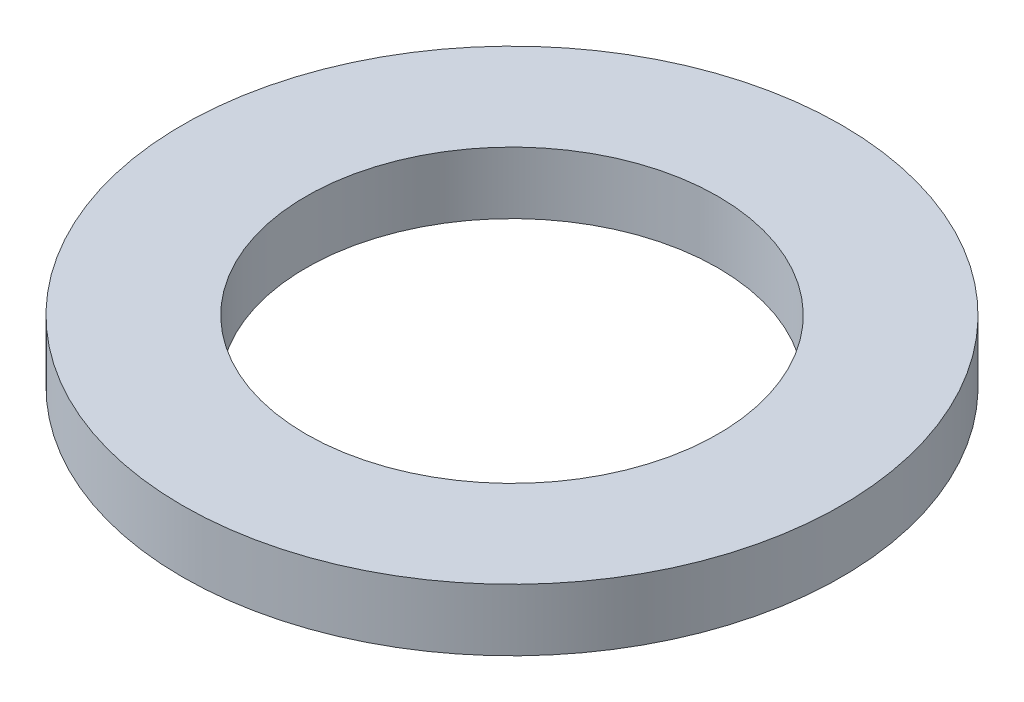
SolidWorks part; units mm, degrees
ref_plane "Front Plane" through (0, 0, 0) normal (0, 0, 1) x (1, 0, 0)
ref_plane "Top Plane" through (0, 0, 0) normal (0, 1, 0) x (1, 0, 0)
ref_plane "Right Plane" through (0, 0, 0) normal (1, 0, 0) x (0, 0, -1)
sketch "Sketch1" plane through (0, 0, 0) normal (0, 1, 0) x (1, 0, 0)
  circle A0 centre (0, 0) radius 12.7
  circle A1 centre (0, 0) radius 7.9375
  dimension "D1" = 15.875
  dimension "D2" = 25.4
extrude "Boss-Extrude1" add sketch "Sketch1" along normal blind 2.3876
